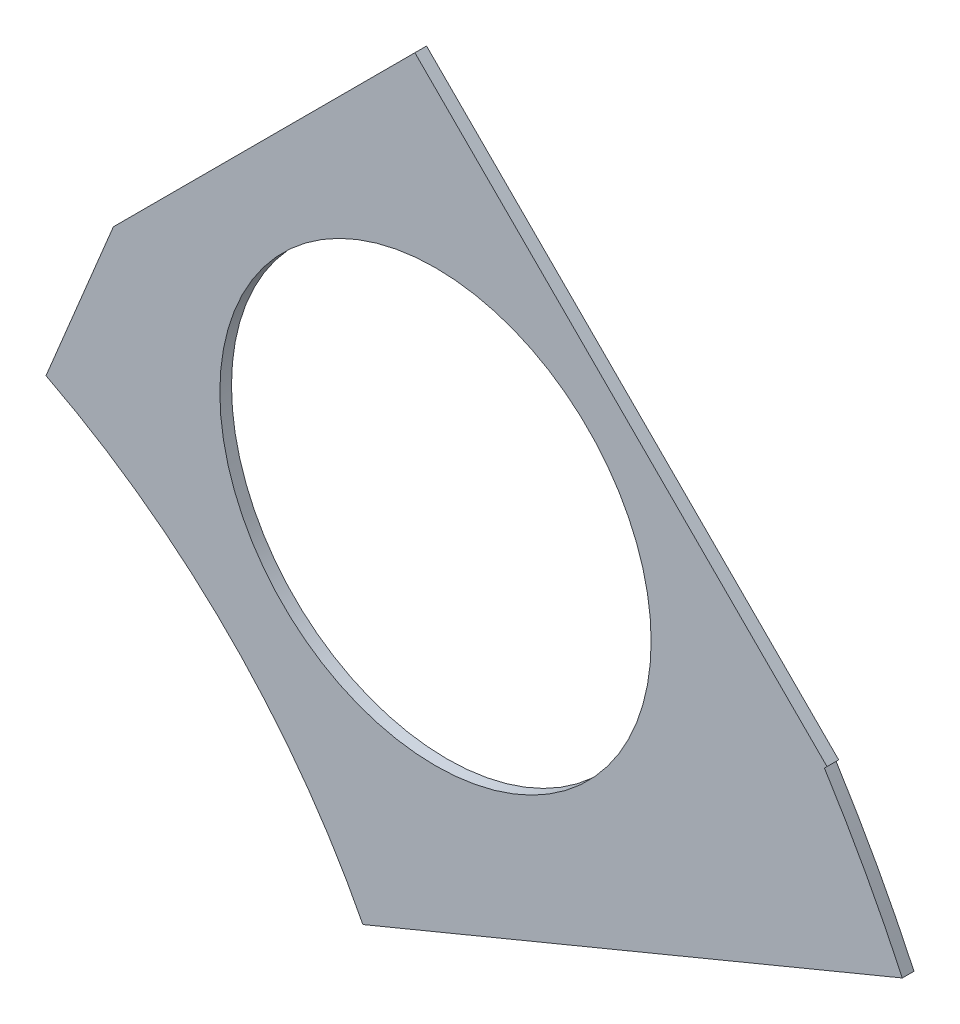
SolidWorks part; units mm, degrees
material "Copper"
ref_plane "Front Plane" through (0, 0, 0) normal (0, 0, 1) x (1, 0, 0)
ref_plane "Top Plane" through (0, 0, 0) normal (0, 1, 0) x (1, 0, 0)
ref_plane "Right Plane" through (0, 0, 0) normal (1, 0, 0) x (0, 0, -1)
sketch "Sketch1" plane through (0, 0, 0) normal (0, 0, 1) x (1, 0, 0)
  line L0 (0, 0) -> (320.3893, 0) construction
  line L1 (0, 0) -> (155.5285, 155.5285) construction
  line L2 (67.2115, 76.1917) -> (8.6967, 17.6769)
  line L3 (8.6967, 17.6769) -> (7.229, 14.1336)
  line L4 (101.4014, -6.35) -> (18.6489, -6.35)
  line L5 (15.1056, -4.8823) -> (18.6489, -6.35)
  line L6 (88.6729, 6.35) -> (27.8605, 6.35)
  line L9 (67.1914, 58.2111) -> (24.1905, 15.2102)
  line L10 (0, 0) -> (40.4486, 97.6516) construction
  line L11 (0, 0) -> (123.4567, -51.1374) construction
  line L18 (8.6967, 17.6769) -> (13.294, 8.6183) construction
  line L19 (18.6489, -6.35) -> (15.4943, 3.3063) construction
  line L20 (27.8605, 6.35) -> (27.7442, 6.7059) construction
  line L21 (24.1905, 15.2102) -> (24.3599, 14.8764) construction
  arc A0 (7.229, 14.1336) -> (15.1056, -4.8823) centre (0, 0) cw
  arc A1 (67.2115, 76.1917) -> (101.4014, -6.35) centre (0, 0) cw
  arc A2 (24.1905, 15.2102) -> (27.8605, 6.35) centre (0, 0) cw
  arc A3 (67.1914, 58.2111) -> (88.6729, 6.35) centre (0, 0) cw
  arc A8 (13.294, 8.6183) -> (15.4943, 3.3063) centre (0, 0) cw construction
  arc A9 (24.3599, 14.8764) -> (27.7442, 6.7059) centre (0, 0) cw construction
  dimension "D1" = 45
  dimension "D3" = 6.35
  dimension "D4" = 15.875
  dimension "D7" = 22.5
  dimension "D8" = 101.6
  dimension "D11" = 12.7
  dimension "D12" = 12.7
  dimension "D2" = 6.35
  dimension "D5" = 67.5
  dimension "D9" = 1.27
  dimension "D10" = 1.27
  dimension "D6" = 12.7
extrude "Boss-Extrude1" add sketch "Sketch1" along normal blind 0.254
sketch "Sketch2" plane through (0, 0, 0.254) normal (0, 0, 1) x (1, 0, 0)
  line L0 (0, 0) -> (101.6, 0) construction
  line L1 (0, 0) -> (71.842, 71.842) construction
  line L3 (0, 0) -> (22.225, 0) construction
  line L4 (0, 0) -> (15.7154, 15.7154) construction
  line L5 (0, 0) -> (95.25, 0) construction
  line L6 (0, 0) -> (92.0044, 24.6525) construction
  arc A0 (101.4014, -6.35) -> (67.2115, 76.1917) centre (0, 0) ccw construction
  circle A1 centre (22.225, 0) radius 4.699
  arc A2 (15.1056, -4.8823) -> (7.229, 14.1336) centre (0, 0) ccw construction
  circle A3 centre (36.195, 0) radius 4.699
  circle A4 centre (61.722, 0) radius 4.699
  circle A5 centre (75.692, 0) radius 4.699
  circle A6 centre (95.25, 0) radius 4.699
  circle A7 centre (15.7154, 15.7154) radius 4.699
  circle A8 centre (25.5937, 25.5937) radius 4.699
  circle A9 centre (43.644, 43.644) radius 4.699
  circle A10 centre (53.5223, 53.5223) radius 4.699
  circle A11 centre (92.0044, 24.6525) radius 4.699
  circle A12 centre (82.4889, 47.625) radius 4.699
  circle A13 centre (67.3519, 67.3519) radius 4.699
  dimension "D3" = 9.398
  dimension "D1" = 45
  dimension "D2" = 6.35
  dimension "D4" = 6.35
  dimension "D5" = 13.97
  dimension "D7" = 13.97
  dimension "D8" = 19.558
  dimension "D9" = 45
  dimension "D10" = 15
  dimension "D11" = 25.527
  dimension "D6" = 2
extrude "Cut-Extrude1" cut sketch "Sketch2" against normal through all
sketch "Sketch3" plane through (0, 0, 0.254) normal (0, 0, 1) x (1, 0, 0)
  line L0 (15.2664, 24.2467) -> (17.0625, 26.0427)
  line L1 (15.2664, 24.2467) -> (15.7154, 23.7977)
  line L2 (17.0625, 26.0427) -> (17.5115, 25.5937)
  line L3 (15.7154, 23.7977) -> (17.5115, 25.5937)
  line L4 (67.2115, 76.1917) -> (8.6967, 17.6769) construction
  line L5 (44.9911, 53.9713) -> (43.195, 52.1753)
  line L6 (44.9911, 53.9713) -> (45.4401, 53.5223)
  line L7 (43.195, 52.1753) -> (43.644, 51.7263)
  line L8 (45.4401, 53.5223) -> (43.644, 51.7263)
  line L9 (27.94, -6.35) -> (30.48, -6.35)
  line L10 (27.94, -6.35) -> (27.94, -5.715)
  line L11 (30.48, -6.35) -> (30.48, -5.715)
  line L12 (27.94, -5.715) -> (30.48, -5.715)
  line L13 (18.6489, -6.35) -> (101.4014, -6.35) construction
  line L14 (67.437, -6.35) -> (69.977, -6.35)
  line L15 (67.437, -6.35) -> (67.437, -5.715)
  line L16 (69.977, -6.35) -> (69.977, -5.715)
  line L17 (67.437, -5.715) -> (69.977, -5.715)
  line L18 (29.2307, 38.211) -> (31.0268, 40.007)
  line L19 (29.2307, 38.211) -> (29.6797, 37.762)
  line L20 (31.0268, 40.007) -> (31.4758, 39.558)
  line L21 (29.6797, 37.762) -> (31.4758, 39.558)
  line L22 (56.845, 65.8253) -> (55.049, 64.0292)
  line L23 (56.845, 65.8253) -> (57.294, 65.3763)
  line L24 (55.049, 64.0292) -> (55.498, 63.5802)
  line L25 (57.294, 65.3763) -> (55.498, 63.5802)
  line L26 (47.6885, -6.35) -> (50.2285, -6.35)
  line L27 (47.6885, -6.35) -> (47.6885, -5.715)
  line L28 (50.2285, -6.35) -> (50.2285, -5.715)
  line L29 (47.6885, -5.715) -> (50.2285, -5.715)
  line L30 (84.201, -6.35) -> (86.741, -6.35)
  line L31 (84.201, -6.35) -> (84.201, -5.715)
  line L32 (86.741, -6.35) -> (86.741, -5.715)
  line L33 (84.201, -5.715) -> (86.741, -5.715)
  line L34 (0, 0) -> (100.7308, 13.2615) construction
  line L35 (0, 0) -> (93.8662, 38.8806) construction
  line L36 (0, 0) -> (80.6047, 61.8502) construction
  line L37 (0, 0) -> (101.6, 0) construction
  line L38 (99.9355, 14.4377) -> (100.267, 11.9194)
  line L39 (99.9355, 14.4377) -> (101.1946, 14.6035)
  line L40 (100.267, 11.9194) -> (101.5261, 12.0852)
  line L41 (101.1946, 14.6035) -> (101.5261, 12.0852)
  line L42 (99.9355, 14.4377) -> (101.5261, 12.0852) construction
  line L43 (100.267, 11.9194) -> (101.1946, 14.6035) construction
  line L44 (93.7655, 37.4643) -> (94.9388, 37.9503)
  line L45 (93.7655, 37.4643) -> (92.7935, 39.811)
  line L46 (94.9388, 37.9503) -> (93.9668, 40.297)
  line L47 (92.7935, 39.811) -> (93.9668, 40.297)
  line L48 (93.7655, 37.4643) -> (93.9668, 40.297) construction
  line L49 (94.9388, 37.9503) -> (92.7935, 39.811) construction
  line L50 (79.3278, 62.4712) -> (80.874, 60.456)
  line L51 (79.3278, 62.4712) -> (80.3354, 63.2443)
  line L52 (80.874, 60.456) -> (81.8816, 61.2292)
  line L53 (80.3354, 63.2443) -> (81.8816, 61.2292)
  line L54 (79.3278, 62.4712) -> (81.8816, 61.2292) construction
  line L55 (80.874, 60.456) -> (80.3354, 63.2443) construction
  line L56 (13.5939, 7.0054) -> (14.5659, 4.6588)
  line L57 (13.5939, 7.0054) -> (14.7672, 7.4914)
  line L58 (14.5659, 4.6588) -> (15.7393, 5.1448)
  line L59 (14.7672, 7.4914) -> (15.7393, 5.1448)
  line L60 (13.5939, 7.0054) -> (15.7393, 5.1448) construction
  line L61 (14.5659, 4.6588) -> (14.7672, 7.4914) construction
  circle A0 centre (15.7154, 15.7154) radius 4.699 construction
  circle A1 centre (43.644, 43.644) radius 4.699 construction
  circle A2 centre (22.225, 0) radius 4.699 construction
  circle A3 centre (61.722, 0) radius 4.699 construction
  arc A4 (101.4014, -6.35) -> (67.2115, 76.1917) centre (0, 0) ccw construction
  arc A9 (15.1056, -4.8823) -> (7.229, 14.1336) centre (0, 0) ccw construction
  circle A10 centre (36.195, 0) radius 4.699 construction
  circle A11 centre (75.692, 0) radius 4.699 construction
  circle A12 centre (25.5937, 25.5937) radius 4.699 construction
  circle A13 centre (53.5223, 53.5223) radius 4.699 construction
  point P75 (14.6666, 6.0751)
  dimension "D2" = 5.715
  dimension "D3" = 2.54
  dimension "D6" = 5.715
  dimension "D8" = 0.635
  dimension "D9" = 5.715
  dimension "D12" = 5.715
  dimension "D4" = 7.5
  dimension "D5" = 22.5
  dimension "D7" = 37.5
  dimension "D10" = 90
  dimension "D11" = 1.27
  dimension "D14" = 0.635
  dimension "D15" = 90
  dimension "D18" = 0.635
  dimension "D19" = 90
  dimension "D22" = 0.635
  dimension "D20" = 1.27
  dimension "D17" = 0.635
  dimension "D13" = 11.4935
  dimension "D16" = 8.509
  dimension "D21" = 11.4935
  dimension "D23" = 8.509
extrude "Cut-Extrude2" cut sketch "Sketch3" against normal through all
sketch "Sketch5" plane through (0, 0, 0.254) normal (0, 0, 1) x (1, 0, 0)
  line L0 (8.1948, 4.769) -> (26.968, 12.5451)
  line L1 (17.5115, 25.5937) -> (17.0625, 26.0427) construction
  line L2 (15.1056, 4.8823) -> (15.7393, 5.1448) construction
  line L4 (26.968, 12.5451) -> (12.5996, 26.9136)
  line L7 (15.7154, 23.7977) -> (17.5115, 25.5937) construction
  line L8 (12.5996, 26.9136) -> (-0.6751, 13.6389)
  line L9 (-0.6751, 13.6389) -> (8.1948, 4.769)
  dimension "D1" = 2.54
  dimension "D2" = 2.54
  dimension "D3" = 90
  dimension "D4" = 20.32
  dimension "D5" = 90
  dimension "D6" = 20.32
  dimension "D7" = 90
extrude "Cut-Extrude5" cut sketch "Sketch5" against normal through all flip side to cut
equation "\"CoilSep\"= 1.005"
equation "\"D11@Sketch2\"=\"CoilSep\""
equation "\"CoilSep2\"= \"D8@Sketch2\""
equation "\"D13@Sketch3\"=\"CoilSep\"/2-.05"
equation "\"D16@Sketch3\"=\"CoilSep2\"/2-.05"
equation "\"D21@Sketch3\"=\"CoilSep\"/2-.05"
equation "\"D23@Sketch3\"=\"CoilSep2\"/2-.05"
